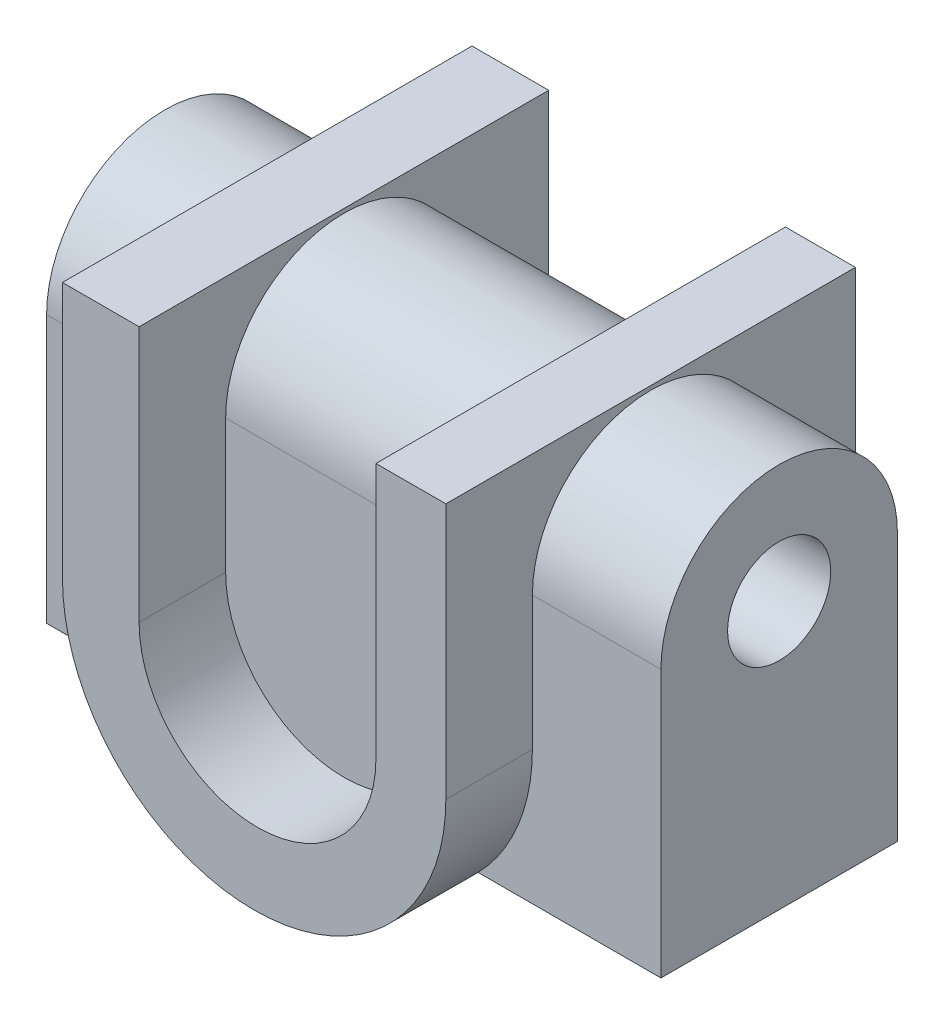
SolidWorks part; units mm, degrees
ref_plane "Front Plane" through (0, 0, 0) normal (0, 0, 1) x (1, 0, 0)
ref_plane "Top Plane" through (0, 0, 0) normal (0, 1, 0) x (1, 0, 0)
ref_plane "Right Plane" through (0, 0, 0) normal (1, 0, 0) x (0, 0, -1)
sketch "Sketch1" plane through (0, 0, 0) normal (0, 0, 1) x (1, 0, 0)
  line L0 (0, 50.0002) -> (0, 0)
  line L1 (46.2557, 0) -> (46.2557, 50.0002)
  line L2 (46.2557, 50.0002) -> (59.9122, 50.0002)
  line L3 (59.9122, 50.0002) -> (59.9122, 0)
  line L4 (-14.978, 0) -> (-14.978, 50.0002)
  line L5 (-14.978, 50.0002) -> (0, 50.0002)
  arc A0 (0, 0) -> (46.2557, 0) centre (23.1279, 0) ccw
  arc A1 (59.9122, 0) -> (-14.978, 0) centre (22.4671, 0) cw
extrude "Boss-Extrude1" add sketch "Sketch1" along normal mid plane 80
sketch "Sketch2" plane through (-14.978, 0, 0) normal (-1, 0, 0) x (0, 0, 1)
  line L1 (-23.096, -26.1078) -> (23.096, -26.1078)
  line L2 (-23.096, -26.1078) -> (-23.096, 26.1078)
  line L4 (23.096, -26.1078) -> (23.096, 26.1078)
  line L5 (-23.096, -26.1078) -> (23.096, 26.1078) construction
  line L6 (-23.096, 26.1078) -> (23.096, -26.1078) construction
  arc A0 (23.096, 26.1078) -> (-23.096, 26.1078) centre (0, 26.1078) ccw
  circle A1 centre (0, 26.1078) radius 10.0769
  point P0 (0, 0)
extrude "Boss-Extrude2" add sketch "Sketch2" against normal blind 100 and the other way blind 20
sketch "Sketch5" plane through (-14.978, 0, 0) normal (-1, 0, 0) x (0, 0, 1)
  circle A0 centre (0, 26.1078) radius 10.0769
extrude "Cut-Extrude1" cut sketch "Sketch5" against normal through all
